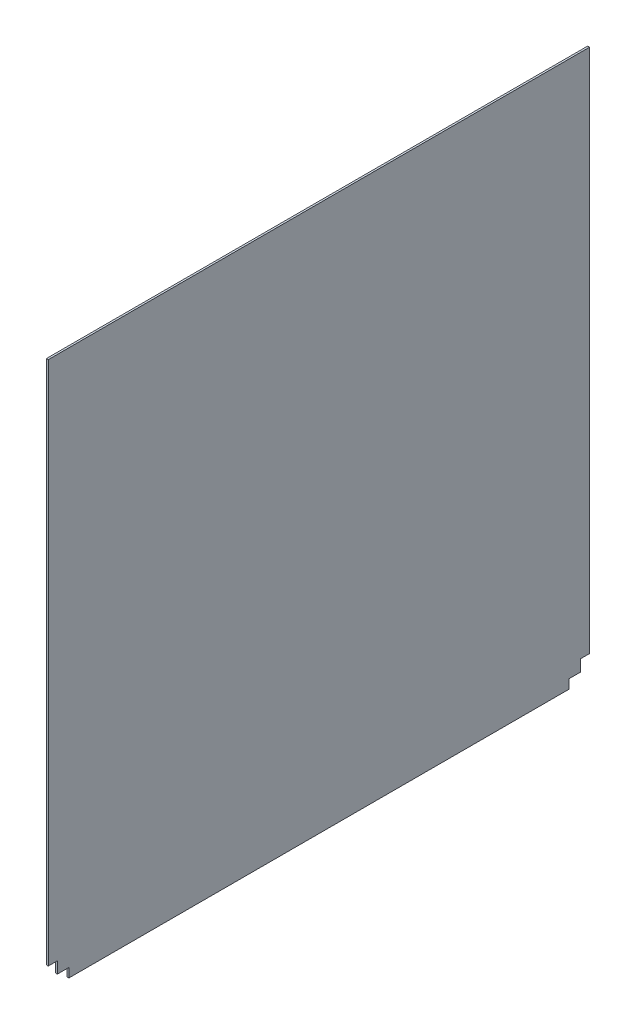
SolidWorks part; units mm, degrees
ref_plane "Front Plane" through (0, 0, 0) normal (0, 0, 1) x (1, 0, 0)
ref_plane "Top Plane" through (0, 0, 0) normal (0, 1, 0) x (1, 0, 0)
ref_plane "Right Plane" through (0, 0, 0) normal (1, 0, 0) x (0, 0, -1)
sketch "Sketch2" plane through (0, 0, 0) normal (1, 0, 0) x (0, 0, -1)
  line L0 (907.001, 34.544) -> (891.761, 34.544)
  line L1 (0, 0) -> (907.001, 0)
  line L2 (0, 0) -> (0, 914.4)
  line L3 (0, 914.4) -> (907.001, 914.4)
  line L4 (907.001, 0) -> (907.001, 914.4)
  line L5 (907.001, 0) -> (914.401, 0) construction
  line L6 (907.001, 0) -> (907.001, 914.4) construction
  line L7 (907.001, 914.4) -> (914.401, 914.4) construction
  line L8 (914.401, 0) -> (914.401, 914.4) construction
  line L57 (891.761, 34.544) -> (891.761, 15.24)
  line L58 (891.761, 15.24) -> (872.457, 15.24)
  line L59 (872.457, 15.24) -> (872.457, 0)
  line L60 (0, 34.544) -> (15.24, 34.544)
  line L61 (15.24, 34.544) -> (15.24, 15.24)
  line L62 (15.24, 15.24) -> (34.544, 15.24)
  line L63 (34.544, 15.24) -> (34.544, 0)
  dimension "D1" = 914.4
  dimension "D2" = 907.001
  dimension "D3" = 7.4
  dimension "D4" = 34.544
  dimension "D5" = 15.24
  dimension "D6" = 15.24
  dimension "D7" = 34.544
  dimension "D8" = 914.401
  dimension "D9" = 914.4
  dimension "D10" = 15.24
  dimension "D11" = 15.24
  dimension "D12" = 34.544
  dimension "D13" = 34.544
extrude "Boss-Extrude4" add sketch "Sketch2" along normal blind 3.175 contours L62 L63 L1 L59 L58 L57 L0 L4 L3 L2 L60 L61
